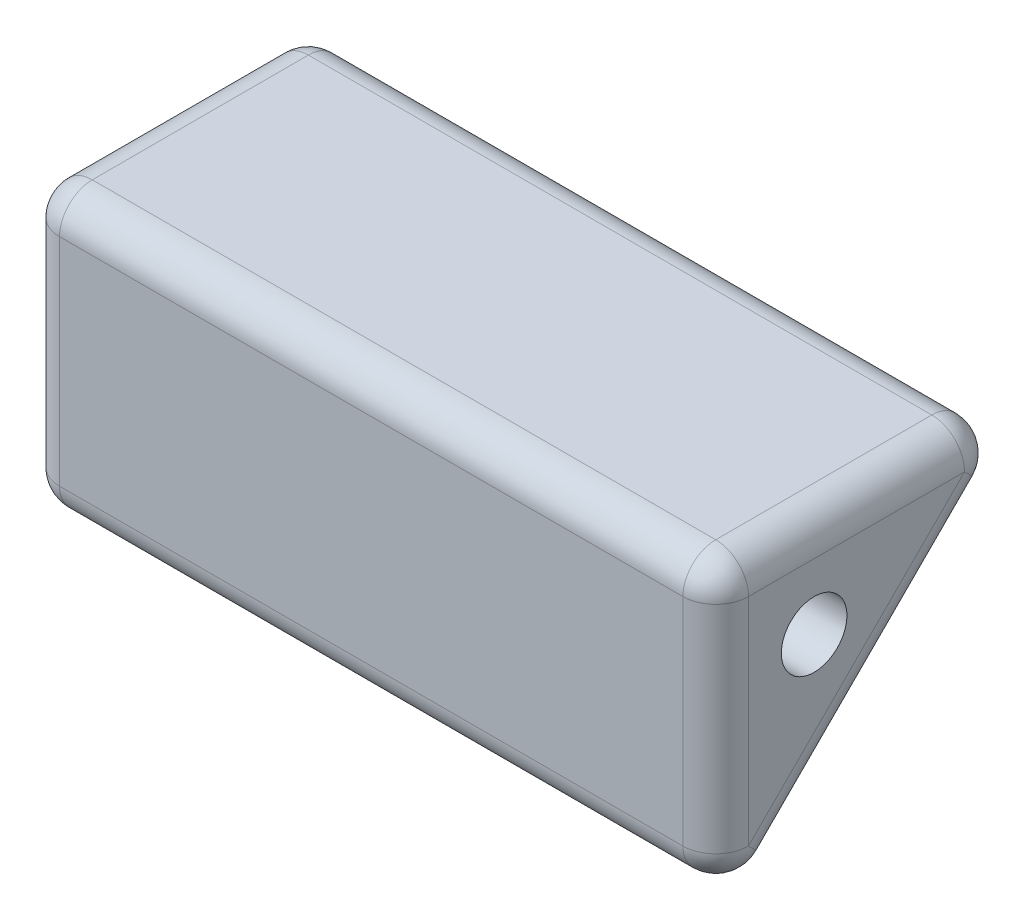
SolidWorks part; units mm, degrees
ref_plane "Front Plane" through (0, 0, 0) normal (0, 0, 1) x (1, 0, 0)
ref_plane "Top Plane" through (0, 0, 0) normal (0, 1, 0) x (1, 0, 0)
ref_plane "Right Plane" through (0, 0, 0) normal (1, 0, 0) x (0, 0, -1)
sketch "Sketch1" plane through (0, 0, 0) normal (1, 0, 0) x (0, 0, -1)
  line L0 (10, 0) -> (0, -10)
  line L1 (0, 0) -> (10, 0)
  line L2 (0, 0) -> (0, -10)
  line L3 (0, -10) -> (10, -10)
  line L4 (10, 0) -> (10, -10)
  dimension "D1" = 10
  dimension "D2" = 10
extrude "body" add sketch "Sketch1" along normal blind 21 contours L1 L2 L0
sketch "Sketch2" plane through (0, 0, 0) normal (-1, 0, 0) x (0, 0, 1)
  line L0 (0, 0) -> (-10, 0) construction
  line L1 (0, 0) -> (0, -10) construction
  circle A0 centre (-3, -3) radius 1
  dimension "D1" = 2
  dimension "D2" = 3
  dimension "D3" = 3
extrude "bolt_hole" cut sketch "Sketch2" against normal through all
fillet "edge_fillets" radius 1 9 edges at (21, 0, -5) (0, 0, -5) (10.5, 0, 0) (21, -5, 0) (0, -5, 0) (10.5, -10, 0) (21, -5, -5) (10.5, 0, -10) (0, -5, -5)
